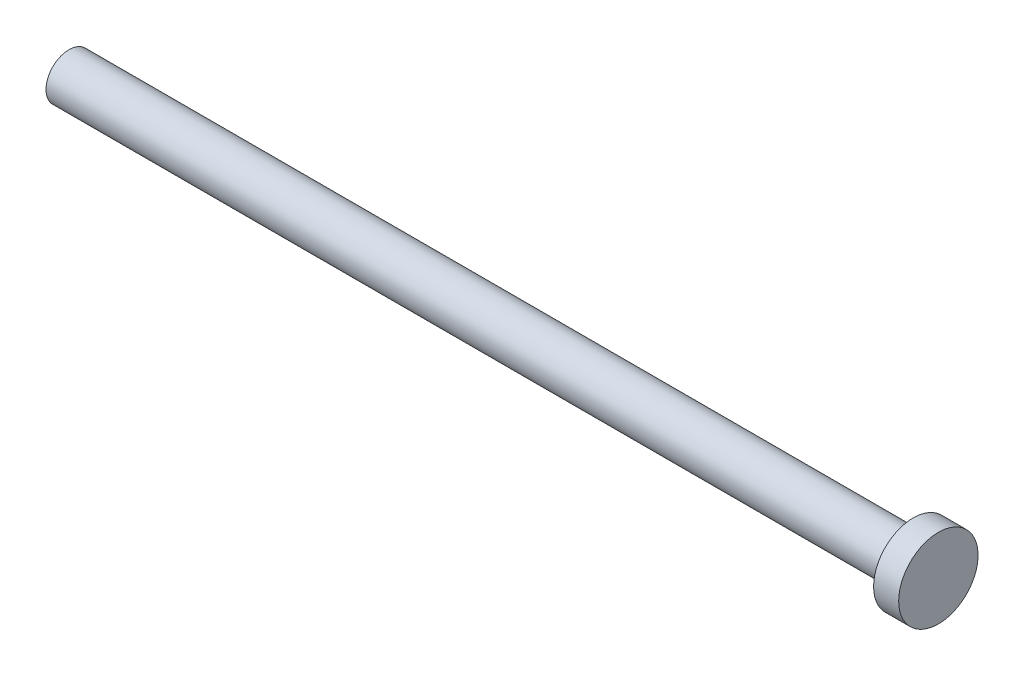
SolidWorks part; units mm, degrees
material "Alloy Steel"
ref_plane "Front Plane" through (0, 0, 0) normal (0, 0, 1) x (1, 0, 0)
ref_plane "Top Plane" through (0, 0, 0) normal (0, 1, 0) x (1, 0, 0)
ref_plane "Right Plane" through (0, 0, 0) normal (1, 0, 0) x (0, 0, -1)
sketch "Sketch1" plane through (0, 0, 0) normal (0, 0, 1) x (1, 0, 0)
  line L0 (-101.5479, 0) -> (76.0222, 0) construction
  line L1 (-26.416, 0) -> (26.416, 0)
  line L2 (26.416, 0) -> (26.416, 2.413)
  line L3 (26.416, 2.413) -> (24.892, 2.413)
  line L4 (24.892, 2.413) -> (24.892, 1.397)
  line L5 (24.892, 1.397) -> (-26.416, 1.397)
  line L6 (-26.416, 1.397) -> (-26.416, 0)
  line L7 (-26.416, 0) -> (-26.416, 0.1593)
  dimension "D1" = 52.832
  dimension "D2" = 1.524
  dimension "D3" = 1.397
  dimension "D4" = 2.413
revolve "Revolve1" add sketch "Sketch1" angle 360 about L0
